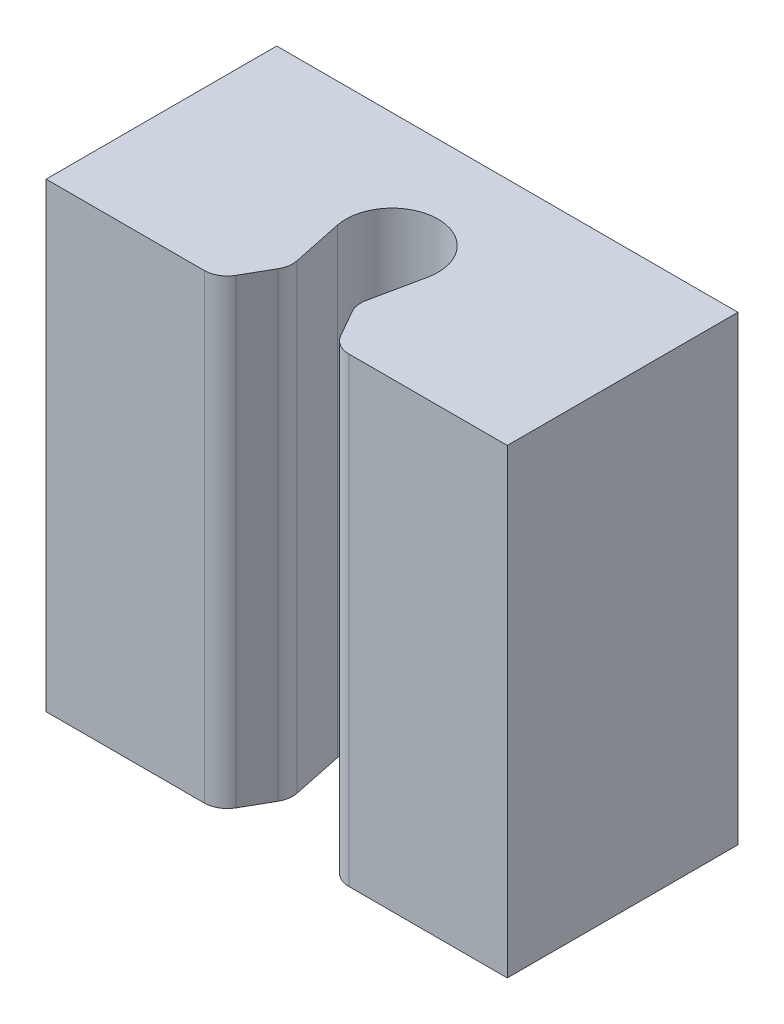
SolidWorks part; units mm, degrees
ref_plane "Ebene vorne" through (0, 0, 0) normal (0, 0, 1) x (1, 0, 0)
ref_plane "Ebene oben" through (0, 0, 0) normal (0, 1, 0) x (1, 0, 0)
ref_plane "Ebene rechts" through (0, 0, 0) normal (1, 0, 0) x (0, 0, -1)
sketch "Skizze1" plane through (0, 0, 0) normal (0, 0, 1) x (1, 0, 0)
  line L1 (50, 50) -> (-50, 50)
  line L2 (50, 50) -> (50, -50)
  line L3 (50, -50) -> (-50, -50)
  line L4 (-50, 50) -> (-50, -50)
  line L5 (50, 50) -> (-50, -50) construction
  line L6 (50, -50) -> (-50, 50) construction
  point P0 (0, 0)
  dimension "D1" = 100
  dimension "D2" = 100
extrude "Aufsatz-Linear austragen1" add sketch "Skizze1" along normal blind 50
sketch "Skizze2" plane through (0, -50, 0) normal (0, -1, 0) x (1, 0, 0)
  line L0 (-9.7893, 27.0421) -> (-5, 50)
  line L1 (-5, 50) -> (5, 50)
  line L2 (5, 50) -> (9.7893, 27.0421)
  line L3 (0, 25) -> (0, 50) construction
  line L4 (-50, 50) -> (50, 50) construction
  line L5 (-7.0861, 40) -> (-12.7902, 50)
  line L6 (-12.7902, 50) -> (12.7902, 50)
  line L7 (12.7902, 50) -> (7.0861, 40)
  circle A0 centre (0, 25) radius 10
  dimension "D2" = 20
  dimension "D1" = 25
  dimension "D3" = 10
  dimension "D4" = 25.5803
  dimension "D5" = 10
extrude "Schnitt-Linear austragen1" cut sketch "Skizze2" against normal through all
fillet "Verrundung1" radius 5 4 edges at (12.7902, 0, 50) (7.0861, 0, 40) (-12.7901, 0, 50) (-7.0861, 0, 40)
